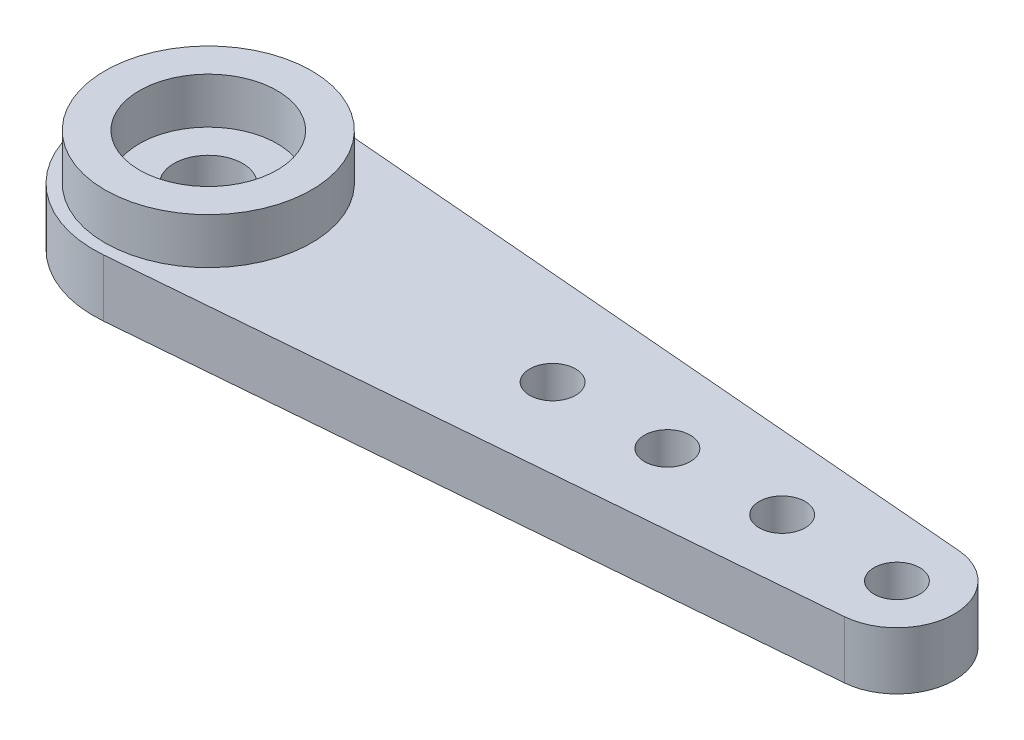
SolidWorks part; units mm, degrees
material "1060 Alloy"
ref_plane "Front Plane" through (0, 0, 0) normal (0, 0, 1) x (1, 0, 0)
ref_plane "Top Plane" through (0, 0, 0) normal (0, 1, 0) x (1, 0, 0)
ref_plane "Right Plane" through (0, 0, 0) normal (1, 0, 0) x (0, 0, -1)
sketch "Sketch1" plane through (0, 0, 0) normal (0, 1, 0) x (1, 0, 0)
  line L0 (0, 0) -> (-30, 0) construction
  line L1 (-29.5833, 4.9826) -> (0.2083, 2.4913)
  line L2 (-29.5833, -4.9826) -> (0.2083, -2.4913)
  line L3 (-5, 0) -> (-35, 0) construction
  line L4 (-10, 0) -> (-40, 0) construction
  line L5 (-15, 0) -> (-45, 0) construction
  circle A0 centre (-30, 0) radius 5
  circle A1 centre (0, 0) radius 2.5
  circle A2 centre (0, 0) radius 1
  circle A6 centre (-5, 0) radius 1
  circle A7 centre (-10, 0) radius 1
  circle A8 centre (-15, 0) radius 1
  dimension "D1" = 10
  dimension "D2" = 5
  dimension "D4" = 2
  dimension "D3" = 30
  dimension "D6" = 5
  dimension "D5" = 4
extrude "Boss-Extrude1" add sketch "Sketch1" along normal blind 2.5
sketch "Sketch2" plane through (0, 2.5, 0) normal (0, 1, 0) x (1, 0, 0)
  circle A0 centre (-30, 0) radius 4.5
  circle A1 centre (-30, 0) radius 3
  dimension "D1" = 9
  dimension "D2" = 6
extrude "Boss-Extrude2" add sketch "Sketch2" along normal blind 2
sketch "Sketch3" plane through (0, 2.5, 0) normal (0, 1, 0) x (1, 0, 0)
  circle A0 centre (-30, 0) radius 1.5
  dimension "D1" = 3
extrude "Cut-Extrude1" cut sketch "Sketch3" against normal through all
sketch "Sketch4" plane through (0, 0, 0) normal (0, -1, 0) x (1, 0, 0)
  circle A0 centre (-30, 0) radius 3.5
  dimension "D1" = 7
extrude "Cut-Extrude2" cut sketch "Sketch4" against normal blind 0.2
